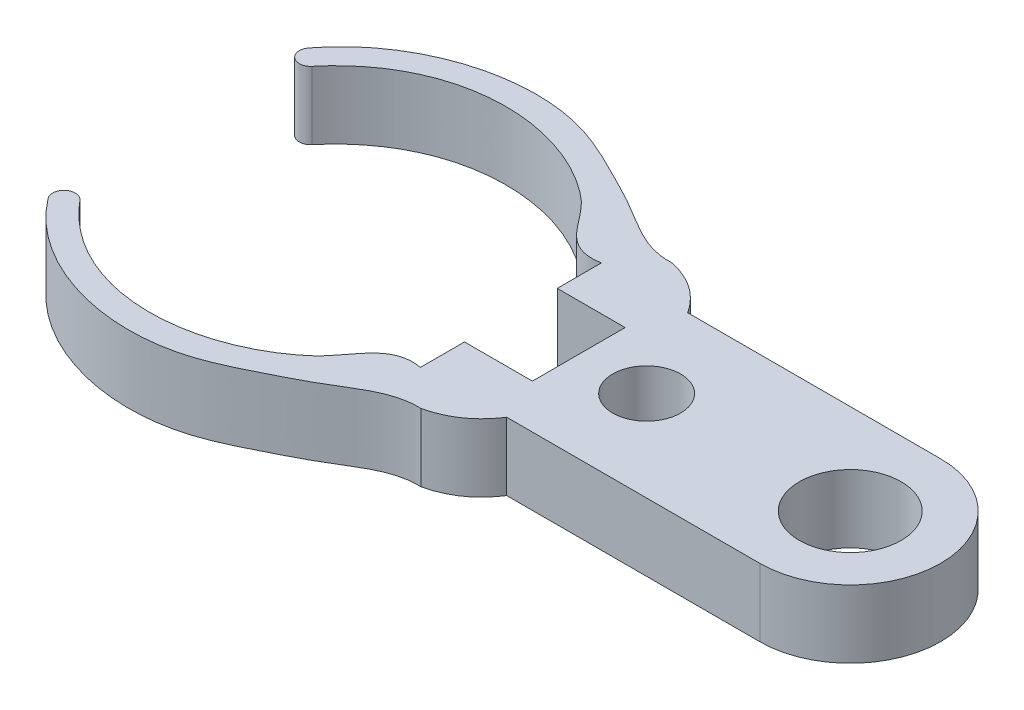
SolidWorks part; units mm, degrees
ref_plane "Front Plane" through (0, 0, 0) normal (0, 0, 1) x (1, 0, 0)
ref_plane "Top Plane" through (0, 0, 0) normal (0, 1, 0) x (1, 0, 0)
ref_plane "Right Plane" through (0, 0, 0) normal (1, 0, 0) x (0, 0, -1)
sketch "Sketch1" plane through (0, 0, 0) normal (0, 1, 0) x (1, 0, 0)
  line L0 (0, 4) -> (15, 4) construction
  line L1 (0, 0) -> (15, 0)
  line L2 (0, 0) -> (0, 8)
  line L3 (0, 8) -> (15, 8)
  line L4 (15, 0) -> (15, 8)
  line L5 (-13.9234, 9.1252) -> (-14.6796, 9.7795)
  line L7 (0, 6.05) -> (3, 6.05)
  line L8 (0, 6.05) -> (0, 1.95)
  line L9 (0, 1.95) -> (3, 1.95)
  line L10 (3, 6.05) -> (3, 1.95)
  line L11 (0, 6.05) -> (3, 1.95) construction
  line L12 (1.4624, 0) -> (1.5798, -1.5607)
  line L13 (0, 1.95) -> (3, 6.05) construction
  arc A0 (15, 8) -> (15, 0) centre (15, 4) cw
  circle A1 centre (15, 4) radius 2.25
  arc A2 (-14.6796, 9.7795) -> (-13.9234, 9.1252) centre (-14.3015, 9.4523) ccw
  circle A4 centre (-8, 4) radius 7.55 construction
  arc A5 (-14.6796, -1.7795) -> (-13.9234, -1.1252) centre (-14.3015, -1.4523) cw
  circle A6 centre (6, 4) radius 1.5
  spline S0 degree 3 poles (0, 8) (-1.445, 7.7316) (-1.9898, 9.2748) (-5.9964, 12.5325) (-11.0436, 12.5964) (-13.9234, 9.1252) knots 0 0 0 0 0.216898 0.270831 1 1 1 1
  spline S1 degree 3 poles (0, 0) (-1.445, 0.2684) (-1.9898, -1.2748) (-5.9964, -4.5325) (-11.0436, -4.5964) (-13.9234, -1.1252) knots 0 0 0 0 0.216898 0.270831 1 1 1 1
  spline S2 degree 3 poles (-14.6796, 9.7795) (-12.6289, 12.4741) (-7.7143, 13.9514) (-3.3453, 11.7401) (-1.0056, 10.5602) (0.3946, 9.5012) (1.5798, 9.5607) knots 0 0 0 0 0.557353 0.711947 0.815566 1 1 1 1
  spline S3 degree 3 poles (-14.6796, -1.7795) (-12.6289, -4.4741) (-7.7143, -5.9514) (-3.3453, -3.7401) (-1.0056, -2.5602) (0.3946, -1.5012) (1.5798, -1.5607) knots 0 0 0 0 0.557353 0.711947 0.815566 1 1 1 1
  spline S4 degree 2 poles (1.5798, 9.5607) (3.0164, 9.232) (3.8125, 8) knots 0 0 0 1 1 1
  spline S5 degree 2 poles (1.5798, -1.5607) (3.0164, -1.232) (3.8125, 0) knots 0 0 0 1 1 1
  point P22 (1.5, 4)
  dimension "D3" = 4.5
  dimension "D4" = 15.1
  dimension "D5" = 4
  dimension "D6" = 8
  dimension "D8" = 3
  dimension "D11" = 3
  dimension "D1" = 15
  dimension "D2" = 8
  dimension "D7" = 1
  dimension "D9" = 3
  dimension "D10" = 4.1
extrude "Boss-Extrude1" add sketch "Sketch1" along normal blind 3
